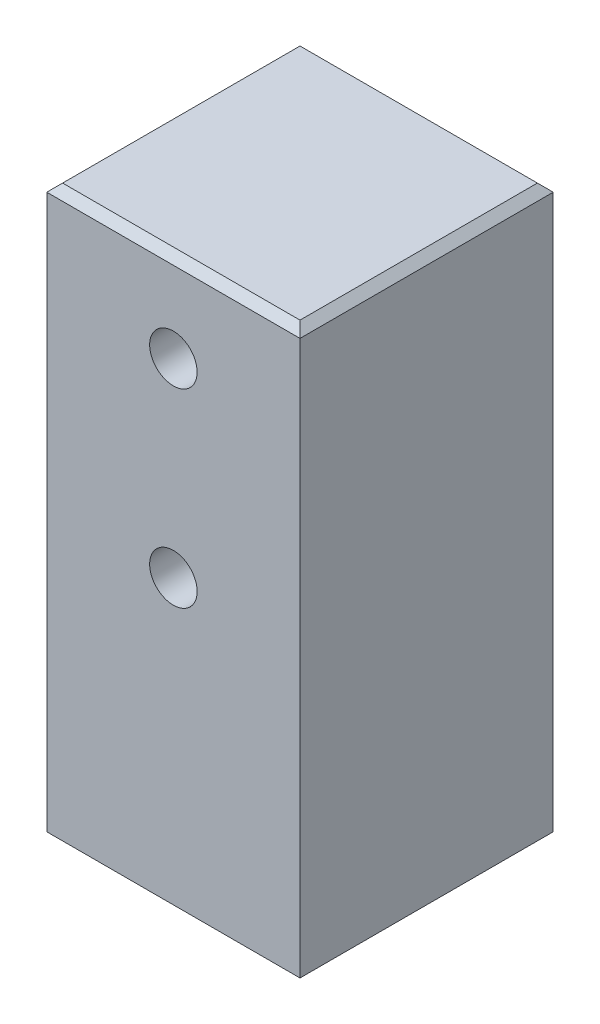
SolidWorks part; units mm, degrees
ref_plane "Front Plane" through (0, 0, 0) normal (0, 0, 1) x (1, 0, 0)
ref_plane "Top Plane" through (0, 0, 0) normal (0, 1, 0) x (1, 0, 0)
ref_plane "Right Plane" through (0, 0, 0) normal (1, 0, 0) x (0, 0, -1)
sketch "Sketch1" plane through (0, 0, 0) normal (0, 1, 0) x (1, 0, 0)
  line L1 (-12.7, 12.7) -> (12.7, 12.7)
  line L2 (-12.7, 12.7) -> (-12.7, -12.7)
  line L3 (-12.7, -12.7) -> (12.7, -12.7)
  line L4 (12.7, 12.7) -> (12.7, -12.7)
  line L5 (-12.7, 12.7) -> (12.7, -12.7) construction
  line L6 (-12.7, -12.7) -> (12.7, 12.7) construction
  point P0 (0, 0)
  dimension "D1" = 25.4
extrude "Boss-Extrude1" add sketch "Sketch1" along normal mid plane 57.15
sketch "Sketch2" plane through (0, -28.575, 0) normal (0, -1, 0) x (-1, 0, 0)
  circle A0 centre (0, 0) radius 3.175
  dimension "D1" = 6.35
extrude "Cut-Extrude1" cut sketch "Sketch2" against normal blind 16.51
sketch "Sketch5" plane through (0, 0, 0) normal (0, 0, 1) x (1, 0, 0)
  line L0 (-3.175, -12.065) -> (3.175, -12.065) construction
  circle A0 centre (0, 0.635) radius 2.3812
  circle A1 centre (0, 19.685) radius 2.3813
  dimension "D1" = 4.7625
  dimension "D2" = 19.05
  dimension "D3" = 12.7
extrude "Cut-Extrude3" cut sketch "Sketch5" against normal through all both and the other way through all
chamfer "Chamfer1" distance 0.7937 angle 45 8 edges at (0, -28.575, -12.7) (-12.7, -28.575, 0) (0, -28.575, 12.7) (12.7, -28.575, 0) (0, 28.575, 12.7) (-12.7, 28.575, 0) (0, 28.575, -12.7) (12.7, 28.575, 0)
sketch "Sketch6" plane through (0, -28.575, 0) normal (0, -1, 0) x (-1, 0, 0)
  circle A0 centre (-5.6569, 5.6569) radius 1.3525
  circle A1 centre (5.6569, 5.6569) radius 1.3525
  circle A2 centre (5.6569, -5.6569) radius 1.3525
  circle A3 centre (-5.6569, -5.6569) radius 1.3525
  circle A4 centre (-5.6569, -5.6569) radius 1.3525 construction
  circle A5 centre (5.6569, -5.6569) radius 1.3525 construction
  circle A6 centre (5.6569, 5.6569) radius 1.3525 construction
  circle A7 centre (-5.6569, 5.6569) radius 1.3525 construction
extrude "Cut-Extrude4" cut sketch "Sketch6" against normal blind 6.35 contours A1 | A2 | A3 | A0
